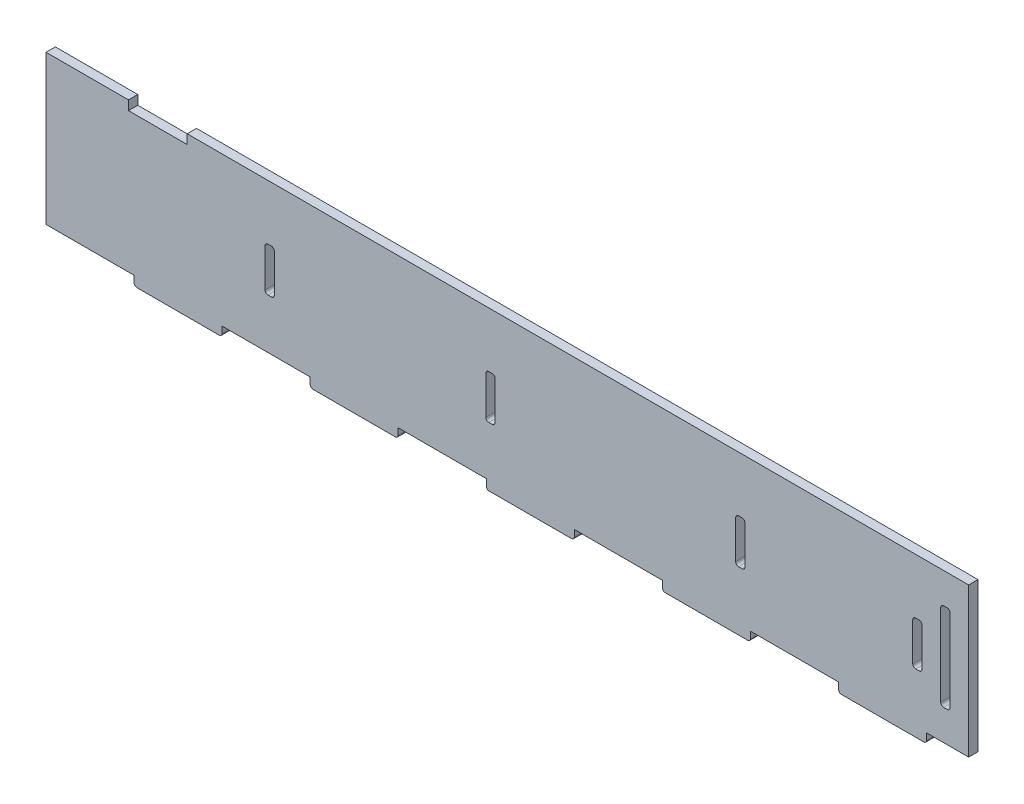
SolidWorks part; units mm, degrees
ref_plane "Front Plane" through (0, 0, 0) normal (0, 0, 1) x (1, 0, 0)
ref_plane "Top Plane" through (0, 0, 0) normal (0, 1, 0) x (1, 0, 0)
ref_plane "Right Plane" through (0, 0, 0) normal (1, 0, 0) x (0, 0, -1)
sketch "Sketch1" plane through (0, 0, 0) normal (0, 0, 1) x (1, 0, 0)
  line L1 (-157.165, -25.4) -> (157.165, -25.4)
  line L2 (-157.165, -25.4) -> (-157.165, 25.4)
  line L3 (-157.165, 25.4) -> (157.165, 25.4)
  line L4 (157.165, -25.4) -> (157.165, 25.4)
  line L5 (-157.165, -25.4) -> (157.165, 25.4) construction
  line L6 (-157.165, 25.4) -> (157.165, -25.4) construction
  point P0 (0, 0)
  dimension "D1" = 314.33
  dimension "D2" = 50.8
extrude "Boss-Extrude1" add sketch "Sketch1" along normal blind 3.175
sketch "Sketch2" plane through (0, 0, 3.175) normal (0, 0, 1) x (1, 0, 0)
  line L0 (-82.55, -25.4) -> (-82.55, -8.4) construction
  line L1 (-157.165, -25.4) -> (157.165, -25.4) construction
  line L2 (-82.55, -8.4) -> (-157.165, -8.4) construction
  line L3 (-157.165, 25.4) -> (-157.165, -25.4) construction
  line L4 (-79.375, -8.4) -> (-7.325, -8.4) construction
  line L5 (-82.55, -8.4) -> (-79.375, -8.4)
  line L6 (-82.55, -8.4) -> (-82.55, 6.6)
  line L7 (-82.55, 6.6) -> (-79.375, 6.6)
  line L8 (-79.375, -8.4) -> (-79.375, 6.6)
  line L10 (-7.325, -8.4) -> (-4.15, -8.4)
  line L11 (-7.325, -8.4) -> (-7.325, 6.6)
  line L12 (-7.325, 6.6) -> (-4.15, 6.6)
  line L13 (-4.15, -8.4) -> (-4.15, 6.6)
  dimension "D1" = 17
  dimension "D2" = 74.615
  dimension "D3" = 15
  dimension "D4" = 3.175
  dimension "D5" = 15
  dimension "D6" = 3.175
  dimension "D7" = 72.05
extrude "Cut-Extrude1" cut sketch "Sketch2" against normal through all
sketch "Sketch3" plane through (0, -25.4, 0) normal (0, -1, 0) x (1, 0, 0)
  line L0 (-157.165, 3.175) -> (157.165, 3.175) construction
  line L1 (-127.165, 3.175) -> (-97.165, 3.175)
  line L2 (-127.165, 3.175) -> (-127.165, 0)
  line L3 (-127.165, 0) -> (-97.165, 0)
  line L4 (-97.165, 3.175) -> (-97.165, 0)
  line L5 (-157.165, 0) -> (157.165, 0) construction
  line L6 (-157.165, 3.175) -> (-157.165, 0) construction
  line L7 (-67.165, 3.175) -> (-67.165, 0)
  line L8 (-67.165, 3.175) -> (-37.165, 3.175)
  line L9 (-37.165, 3.175) -> (-37.165, 0)
  line L10 (-7.165, 3.175) -> (-7.165, 0)
  line L11 (-7.165, 3.175) -> (22.835, 3.175)
  line L12 (22.835, 3.175) -> (22.835, 0)
  line L13 (52.835, 3.175) -> (52.835, 0)
  line L14 (52.835, 3.175) -> (82.835, 3.175)
  line L15 (82.835, 3.175) -> (82.835, 0)
  line L16 (112.835, 3.175) -> (112.835, 0)
  line L17 (112.835, 3.175) -> (142.835, 3.175)
  line L18 (142.835, 3.175) -> (142.835, 0)
  line L19 (-127.165, 3.175) -> (-67.165, 3.175) construction
  line M5 (-157.165, 0) -> (157.165, 0)
  line M7 (157.165, 3.175) -> (-157.165, 3.175)
  dimension "D1" = 30
  dimension "D2" = 30
  dimension "D4" = 60
  dimension "D3" = 5
extrude "Boss-Extrude2" add sketch "Sketch3" along normal blind 3.175 contours L4 L2 M7 M5 | L9 L7 M7 M5 | L18 L16 M7 M5 | L15 L13 M7 M5 | L12 L10 M7 M5
sketch "Sketch4" plane through (0, 0, 3.175) normal (0, 0, 1) x (1, 0, 0)
  line L0 (82.835, -25.4) -> (112.835, -25.4) construction
  line L10 (157.165, -25.4) -> (157.165, 25.4) construction
  line L11 (147.64, 15) -> (150.815, 15)
  line L12 (147.64, 15) -> (147.64, -15)
  line L13 (147.64, -15) -> (150.815, -15)
  line L14 (150.815, 15) -> (150.815, -15)
  line L16 (150.815, 0) -> (157.165, 0) construction
  line L17 (141.285, 25.4) -> (141.285, -25.4) construction
  line L18 (157.165, 25.4) -> (-157.165, 25.4) construction
  line L19 (142.835, -25.4) -> (157.165, -25.4) construction
  line L21 (141.285, 6.6) -> (138.11, 6.6)
  line L22 (141.285, 6.6) -> (141.285, -8.4)
  line L23 (141.285, -8.4) -> (138.11, -8.4)
  line L24 (138.11, 6.6) -> (138.11, -8.4)
  line L25 (80.96, 6.6) -> (77.785, 6.6)
  line L26 (80.96, 6.6) -> (80.96, -8.4)
  line L27 (80.96, -8.4) -> (77.785, -8.4)
  line L28 (77.785, 6.6) -> (77.785, -8.4)
  point P4 (139.6975, -8.4)
  dimension "D1" = 6.35
  dimension "D2" = 3.175
  dimension "D3" = 30
  dimension "D4" = 15.88
  dimension "D5" = 3.175
  dimension "D6" = 15
  dimension "D7" = 15
  dimension "D8" = 3.175
  dimension "D9" = 57.15
  dimension "D10" = 17
  dimension "D11" = 17
extrude "Cut-Extrude2" cut sketch "Sketch4" against normal through all
sketch "Sketch5" plane through (0, 0, 3.175) normal (0, 0, 1) x (1, 0, 0)
  line L0 (157.165, 25.4) -> (-157.165, 25.4) construction
  line L1 (-129.065, 25.4) -> (-109.065, 25.4)
  line L2 (-129.065, 25.4) -> (-129.065, 22.225)
  line L3 (-129.065, 22.225) -> (-109.065, 22.225)
  line L4 (-109.065, 25.4) -> (-109.065, 22.225)
  line L5 (-157.165, 25.4) -> (-157.165, -25.4) construction
  point P6 (-119.065, 25.4)
  dimension "D1" = 3.175
  dimension "D2" = 20
  dimension "D3" = 28.1
extrude "Cut-Extrude3" cut sketch "Sketch5" against normal through all
fillet "Fillet1" radius 1 30 edges at (112.835, -28.575, 1.5875) (142.835, -28.575, 1.5875) (82.835, -28.575, 1.5875) (52.835, -28.575, 1.5875) (22.835, -28.575, 1.5875) (-7.165, -28.575, 1.5875) (-37.165, -28.575, 1.5875) (-67.165, -28.575, 1.5875) (-97.165, -28.575, 1.5875) (-127.165, -28.575, 1.5875) (-79.375, 6.6, 1.5875) (-82.55, 6.6, 1.5875) (-82.55, -8.4, 1.5875) (-79.375, -8.4, 1.5875) (-4.15, -8.4, 1.5875) (-7.325, -8.4, 1.5875) (-7.325, 6.6, 1.5875) (-4.15, 6.6, 1.5875) (80.96, 6.6, 1.5875) (77.785, 6.6, 1.5875) (77.785, -8.4, 1.5875) (80.96, -8.4, 1.5875) (141.285, -8.4, 1.5875) (138.11, -8.4, 1.5875) (138.11, 6.6, 1.5875) (141.285, 6.6, 1.5875) (150.815, 15, 1.5875) (147.64, 15, 1.5875) (150.815, -15, 1.5875) (147.64, -15, 1.5875)
